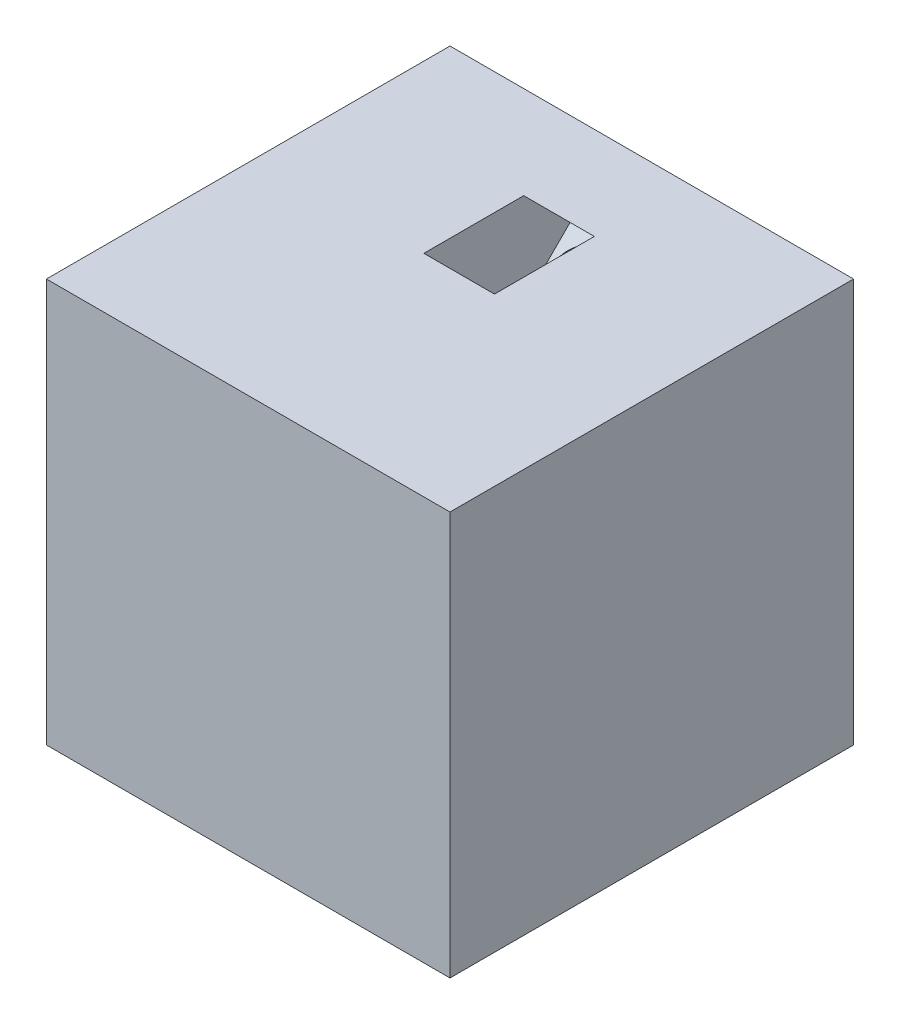
SolidWorks part; units mm, degrees
ref_plane "Plan de face" through (0, 0, 0) normal (0, 0, 1) x (1, 0, 0)
ref_plane "Plan de dessus" through (0, 0, 0) normal (0, 1, 0) x (1, 0, 0)
ref_plane "Plan de droite" through (0, 0, 0) normal (1, 0, 0) x (0, 0, -1)
sketch "Esquisse1" plane through (0, 0, 0) normal (0, 0, 1) x (1, 0, 0)
  line L1 (-121.1641, 35.6452) -> (-81.1641, 35.6452)
  line L2 (-121.1641, 35.6452) -> (-121.1641, -4.3548)
  line L3 (-121.1641, -4.3548) -> (-81.1641, -4.3548)
  line L4 (-81.1641, 35.6452) -> (-81.1641, -4.3548)
  dimension "D1" = 40
  dimension "D2" = 40
extrude "Boss.-Extru.1" add sketch "Esquisse1" along normal blind 40
ref_plane "Plan1" through (0, 17.8226, 17.8226) normal (0, 0.7071, 0.7071) x (1, 0, 0)
sketch "Esquisse2" plane through (0, 17.8226, 17.8226) normal (0, 0.7071, 0.7071) x (1, 0, 0)
  line L0 (-81.1641, 25.2049) -> (-121.1641, 25.2049) construction
  line L1 (-121.1641, -3.0793) -> (-121.1641, 25.2049) construction
  circle A0 centre (-101.1641, 15.2049) radius 3
  dimension "D1" = 6
  dimension "D2" = 10
  dimension "D3" = 20
extrude "Enlèv. mat.-Extru.3" cut sketch "Esquisse2" against normal through all both and the other way through all
sketch "Esquisse4" plane through (0, 17.8226, 17.8226) normal (0, 0.7071, 0.7071) x (1, 0, 0)
  line L0 (-81.1641, -3.0793) -> (-81.1641, 25.2049) construction
  line L1 (-97.6641, 11.7049) -> (-104.6641, 11.7049)
  line L2 (-97.6641, 11.7049) -> (-97.6641, 18.7049)
  line L3 (-97.6641, 18.7049) -> (-104.6641, 18.7049)
  line L4 (-104.6641, 11.7049) -> (-104.6641, 18.7049)
  line L6 (-97.6641, 11.7049) -> (-104.6641, 18.7049) construction
  line L7 (-104.6641, 11.7049) -> (-97.6641, 18.7049) construction
  line L8 (-81.1641, 25.2049) -> (-121.1641, 25.2049) construction
  point P6 (-101.1641, 15.2049)
  point P9 (-101.1641, 25.2049)
  dimension "D1" = 7
  dimension "D2" = 7
  dimension "D3" = 16.5
  dimension "D4" = 10
extrude "Enlèv. mat.-Extru.5" cut sketch "Esquisse4" along normal blind 23.5
ref_plane "Plan5" through (-60.5821, 0, 60.5821) normal (0.7071, 0, -0.7071) x (-0.7071, 0, -0.7071)
sketch "Esquisse6" plane through (-60.5821, 0, 60.5821) normal (0.7071, 0, -0.7071) x (-0.7071, 0, -0.7071)
  line L0 (57.3917, 35.6452) -> (85.676, 35.6452) construction
  line L1 (85.676, 35.6452) -> (85.676, -4.3548) construction
  circle A0 centre (75.676, 5.6452) radius 3
  dimension "D1" = 6
  dimension "D2" = 30
  dimension "D3" = 10
extrude "Enlèv. mat.-Extru.6" cut sketch "Esquisse6" against normal through all both and the other way through all
sketch "Esquisse7" plane through (-60.5821, 0, 60.5821) normal (0.7071, 0, -0.7071) x (-0.7071, 0, -0.7071)
  line L0 (57.3917, 35.6452) -> (85.676, 35.6452) construction
  line L1 (72.176, 9.1452) -> (79.176, 9.1452)
  line L2 (72.176, 9.1452) -> (72.176, 2.1452)
  line L3 (72.176, 2.1452) -> (79.176, 2.1452)
  line L4 (79.176, 9.1452) -> (79.176, 2.1452)
  line L5 (72.176, 9.1452) -> (79.176, 2.1452) construction
  line L6 (85.676, 35.6452) -> (85.676, -4.3548) construction
  point P6 (75.676, 5.6452)
  dimension "D1" = 7
  dimension "D2" = 7
  dimension "D3" = 26.5
  dimension "D4" = 10
extrude "Enlèv. mat.-Extru.7" cut sketch "Esquisse7" against normal blind 23.5
